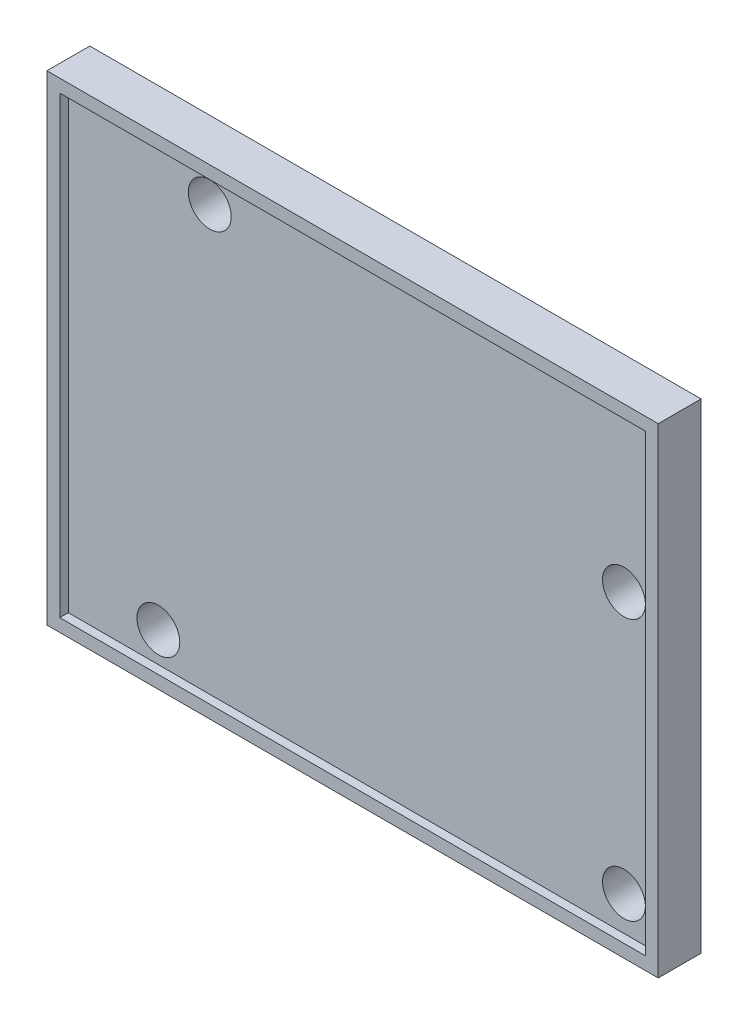
SolidWorks part; units mm, degrees
ref_plane "Front Plane" through (0, 0, 0) normal (0, 0, 1) x (1, 0, 0)
ref_plane "Top Plane" through (0, 0, 0) normal (0, 1, 0) x (1, 0, 0)
ref_plane "Right Plane" through (0, 0, 0) normal (1, 0, 0) x (0, 0, -1)
sketch "Sketch1" plane through (0, 0, 0) normal (0, 0, 1) x (1, 0, 0)
  line L5 (35.655, 28) -> (-35.655, 28)
  line L6 (35.655, 28) -> (35.655, -28)
  line L7 (35.655, -28) -> (-35.655, -28)
  line L8 (-35.655, 28) -> (-35.655, -28)
  line L9 (35.655, 28) -> (-35.655, -28) construction
  line L10 (35.655, -28) -> (-35.655, 28) construction
  point P0 (0, 0)
  dimension "D1" = 71.31
  dimension "D2" = 56
extrude "Boss-Extrude1" add sketch "Sketch1" along normal blind 5 contours L8 L7 L6 L5
sketch "Sketch2" plane through (0, 0, 5) normal (0, 0, 1) x (1, 0, 0)
  line L0 (-35.655, 28) -> (-35.655, -28) construction
  line L1 (35.655, -28) -> (-35.655, -28) construction
  line L2 (35.655, 28) -> (35.655, -28) construction
  line L3 (35.655, 28) -> (-35.655, 28) construction
  circle A0 centre (-23.655, -23) radius 2.5
  circle A1 centre (30.655, 8) radius 2.5
  circle A2 centre (-17.655, 23) radius 2.5
  circle A3 centre (30.655, -22.5) radius 2.5
  dimension "D3" = 5
  dimension "D4" = 5
  dimension "D5" = 5
  dimension "D6" = 5
  dimension "D1" = 12
  dimension "D2" = 5
  dimension "D7" = 5.5
  dimension "D8" = 5
  dimension "D9" = 20
  dimension "D10" = 5
  dimension "D11" = 18
  dimension "D12" = 5
extrude "Cut-Extrude1" cut sketch "Sketch2" against normal blind 5
sketch "Sketch3" plane through (0, 0, 5) normal (0, 0, 1) x (1, 0, 0)
  line L1 (34.155, -26.5) -> (-34.155, -26.5)
  line L2 (34.155, -26.5) -> (34.155, 26.5)
  line L3 (34.155, 26.5) -> (-34.155, 26.5)
  line L4 (-34.155, -26.5) -> (-34.155, 26.5)
  line L5 (34.155, -26.5) -> (-34.155, 26.5) construction
  line L6 (34.155, 26.5) -> (-34.155, -26.5) construction
  point P0 (0, 0)
  dimension "D1" = 53
  dimension "D2" = 68.31
extrude "Cut-Extrude2" cut sketch "Sketch3" against normal blind 1
